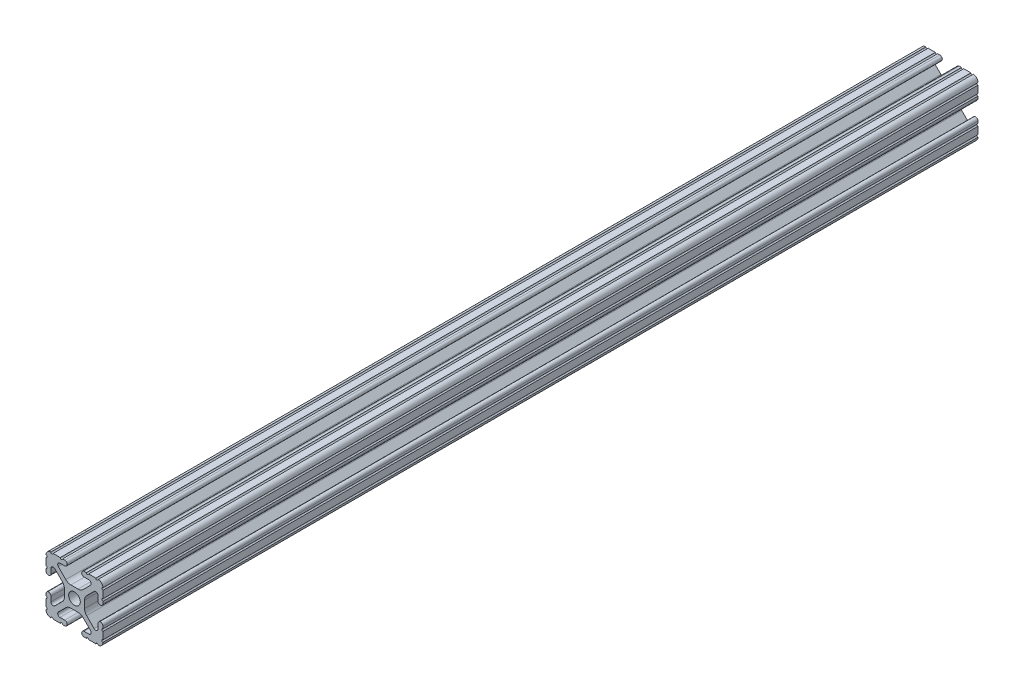
SolidWorks part; units mm, degrees
material "6061-T6 (SS)"
ref_plane "Front Plane" through (0, 0, 0) normal (0, 0, 1) x (1, 0, 0)
ref_plane "Top Plane" through (0, 0, 0) normal (0, 1, 0) x (1, 0, 0)
ref_plane "Right Plane" through (0, 0, 0) normal (1, 0, 0) x (0, 0, -1)
ref_plane "Plane1" through (0, 0, -450.85) normal (0, 0, -1) x (-1, 0, 0)
sketch "Sketch1" plane through (0, 0, -450.85) normal (0, 0, -1) x (-1, 0, 0)
  line L0 (12.7, -9.5504) -> (12.7, -6.3331)
  line L1 (12.7, -5.3171) -> (12.7, -4.3434)
  line L2 (10.4902, -4.3434) -> (10.4902, -6.4748)
  line L3 (8.7558, -7.1932) -> (5.4257, -3.8632)
  line L4 (4.4958, -1.6181) -> (4.4958, 1.6181)
  line L5 (5.4257, 3.8632) -> (8.7558, 7.1932)
  line L6 (10.4902, 6.4748) -> (10.4902, 4.3434)
  line L7 (12.7, 4.3434) -> (12.7, 5.3171)
  line L8 (12.7, 6.3331) -> (12.7, 9.5504)
  line L9 (9.5504, 12.7) -> (6.3331, 12.7)
  line L10 (5.3171, 12.7) -> (4.3434, 12.7)
  line L11 (4.3434, 10.4902) -> (6.4748, 10.4902)
  line L12 (7.1932, 8.7558) -> (3.8632, 5.4257)
  line L13 (1.6181, 4.4958) -> (-1.6181, 4.4958)
  line L14 (-3.8632, 5.4257) -> (-7.1932, 8.7558)
  line L15 (-6.4748, 10.4902) -> (-4.3434, 10.4902)
  line L16 (-4.3434, 12.7) -> (-5.3171, 12.7)
  line L17 (-6.3331, 12.7) -> (-9.5504, 12.7)
  line L18 (-12.7, 9.5504) -> (-12.7, 6.3331)
  line L19 (-12.7, 5.3171) -> (-12.7, 4.3434)
  line L20 (-10.4902, 4.3434) -> (-10.4902, 6.4748)
  line L21 (-8.7558, 7.1932) -> (-5.4257, 3.8632)
  line L22 (-4.4958, 1.6181) -> (-4.4958, -1.6181)
  line L23 (-5.4257, -3.8632) -> (-8.7558, -7.1932)
  line L24 (-10.4902, -6.4748) -> (-10.4902, -4.3434)
  line L25 (-12.7, -4.3434) -> (-12.7, -5.3171)
  line L26 (-12.7, -6.3331) -> (-12.7, -9.5504)
  line L27 (-9.5504, -12.7) -> (-6.3331, -12.7)
  line L28 (-5.3171, -12.7) -> (-4.3434, -12.7)
  line L29 (-4.3434, -10.4902) -> (-6.4748, -10.4902)
  line L30 (-7.1932, -8.7558) -> (-3.8632, -5.4257)
  line L31 (-1.6181, -4.4958) -> (1.6181, -4.4958)
  line L32 (3.8632, -5.4257) -> (7.1932, -8.7558)
  line L33 (6.4748, -10.4902) -> (4.3434, -10.4902)
  line L34 (4.3434, -12.7) -> (5.3171, -12.7)
  line L35 (6.3331, -12.7) -> (9.5504, -12.7)
  arc A0 (12.6998, -10.5664) -> (12.7, -9.5504) centre (12.7, -10.0584) cw
  arc A1 (12.7, -6.3331) -> (12.7, -5.3171) centre (12.7, -5.8251) cw
  arc A2 (12.7, -4.3434) -> (10.4902, -4.3434) centre (11.5951, -4.3434) ccw
  arc A3 (10.4902, -6.4748) -> (8.7558, -7.1932) centre (9.4742, -6.4748) cw
  arc A4 (5.4257, -3.8632) -> (4.4958, -1.6181) centre (7.6708, -1.6181) cw
  arc A5 (4.4958, 1.6181) -> (5.4257, 3.8632) centre (7.6708, 1.6181) cw
  arc A6 (8.7558, 7.1932) -> (10.4902, 6.4748) centre (9.4742, 6.4748) cw
  arc A7 (10.4902, 4.3434) -> (12.7, 4.3434) centre (11.5951, 4.3434) ccw
  arc A8 (12.7, 5.3171) -> (12.7, 6.3331) centre (12.7, 5.8251) cw
  arc A9 (12.7, 9.5504) -> (12.6998, 10.5664) centre (12.7, 10.0584) cw
  arc A10 (12.6998, 10.5664) -> (10.5664, 12.6998) centre (10.5918, 10.5918) ccw
  arc A11 (10.5664, 12.6998) -> (9.5504, 12.7) centre (10.0584, 12.7) cw
  arc A12 (6.3331, 12.7) -> (5.3171, 12.7) centre (5.8251, 12.7) cw
  arc A13 (4.3434, 12.7) -> (4.3434, 10.4902) centre (4.3434, 11.5951) ccw
  arc A14 (6.4748, 10.4902) -> (7.1932, 8.7558) centre (6.4748, 9.4742) cw
  arc A15 (3.8632, 5.4257) -> (1.6181, 4.4958) centre (1.6181, 7.6708) cw
  arc A16 (-1.6181, 4.4958) -> (-3.8632, 5.4257) centre (-1.6181, 7.6708) cw
  arc A17 (-7.1932, 8.7558) -> (-6.4748, 10.4902) centre (-6.4748, 9.4742) cw
  arc A18 (-4.3434, 10.4902) -> (-4.3434, 12.7) centre (-4.3434, 11.5951) ccw
  arc A19 (-5.3171, 12.7) -> (-6.3331, 12.7) centre (-5.8251, 12.7) cw
  arc A20 (-9.5504, 12.7) -> (-10.5664, 12.6998) centre (-10.0584, 12.7) cw
  arc A21 (-10.5664, 12.6998) -> (-12.6998, 10.5664) centre (-10.5918, 10.5918) ccw
  arc A22 (-12.6998, 10.5664) -> (-12.7, 9.5504) centre (-12.7, 10.0584) cw
  arc A23 (-12.7, 6.3331) -> (-12.7, 5.3171) centre (-12.7, 5.8251) cw
  arc A24 (-12.7, 4.3434) -> (-10.4902, 4.3434) centre (-11.5951, 4.3434) ccw
  arc A25 (-10.4902, 6.4748) -> (-8.7558, 7.1932) centre (-9.4742, 6.4748) cw
  arc A26 (-5.4257, 3.8632) -> (-4.4958, 1.6181) centre (-7.6708, 1.6181) cw
  arc A27 (-4.4958, -1.6181) -> (-5.4257, -3.8632) centre (-7.6708, -1.6181) cw
  arc A28 (-8.7558, -7.1932) -> (-10.4902, -6.4748) centre (-9.4742, -6.4748) cw
  arc A29 (-10.4902, -4.3434) -> (-12.7, -4.3434) centre (-11.5951, -4.3434) ccw
  arc A30 (-12.7, -5.3171) -> (-12.7, -6.3331) centre (-12.7, -5.8251) cw
  arc A31 (-12.7, -9.5504) -> (-12.6998, -10.5664) centre (-12.7, -10.0584) cw
  arc A32 (-12.6998, -10.5664) -> (-10.5664, -12.6998) centre (-10.5918, -10.5918) ccw
  arc A33 (-10.5664, -12.6998) -> (-9.5504, -12.7) centre (-10.0584, -12.7) cw
  arc A34 (-6.3331, -12.7) -> (-5.3171, -12.7) centre (-5.8251, -12.7) cw
  arc A35 (-4.3434, -12.7) -> (-4.3434, -10.4902) centre (-4.3434, -11.5951) ccw
  arc A36 (-6.4748, -10.4902) -> (-7.1932, -8.7558) centre (-6.4748, -9.4742) cw
  arc A37 (-3.8632, -5.4257) -> (-1.6181, -4.4958) centre (-1.6181, -7.6708) cw
  arc A38 (1.6181, -4.4958) -> (3.8632, -5.4257) centre (1.6181, -7.6708) cw
  arc A39 (7.1932, -8.7558) -> (6.4748, -10.4902) centre (6.4748, -9.4742) cw
  arc A40 (4.3434, -10.4902) -> (4.3434, -12.7) centre (4.3434, -11.5951) ccw
  arc A41 (5.3171, -12.7) -> (6.3331, -12.7) centre (5.8251, -12.7) cw
  arc A42 (9.5504, -12.7) -> (10.5664, -12.6998) centre (10.0584, -12.7) cw
  arc A43 (10.5664, -12.6998) -> (12.6998, -10.5664) centre (10.5918, -10.5918) ccw
  circle A44 centre (0, 0) radius 2.6035
extrude "Boss-Extrude1" add sketch "Sketch1" against normal mid plane 390.5504
sketch "Sketch2" plane through (0, 0, 0) normal (1, 0, 0) x (0, 0, -1)
  line L0 (255.5748, -12.6998) -> (646.1252, -12.6998) construction
  line L1 (358.7496, -34.6212) -> (542.9504, -34.6212)
  line L2 (358.7496, -34.6212) -> (358.7496, 34.6212)
  line L3 (358.7496, 34.6212) -> (542.9504, 34.6212)
  line L4 (542.9504, -34.6212) -> (542.9504, 34.6212)
  line L5 (358.7496, -34.6212) -> (542.9504, 34.6212) construction
  line L6 (358.7496, 34.6212) -> (542.9504, -34.6212) construction
  point P0 (450.85, 0)
  point P5 (0, 0)
  point P8 (450.85, -12.6998)
  dimension "D1" = 184.2008
